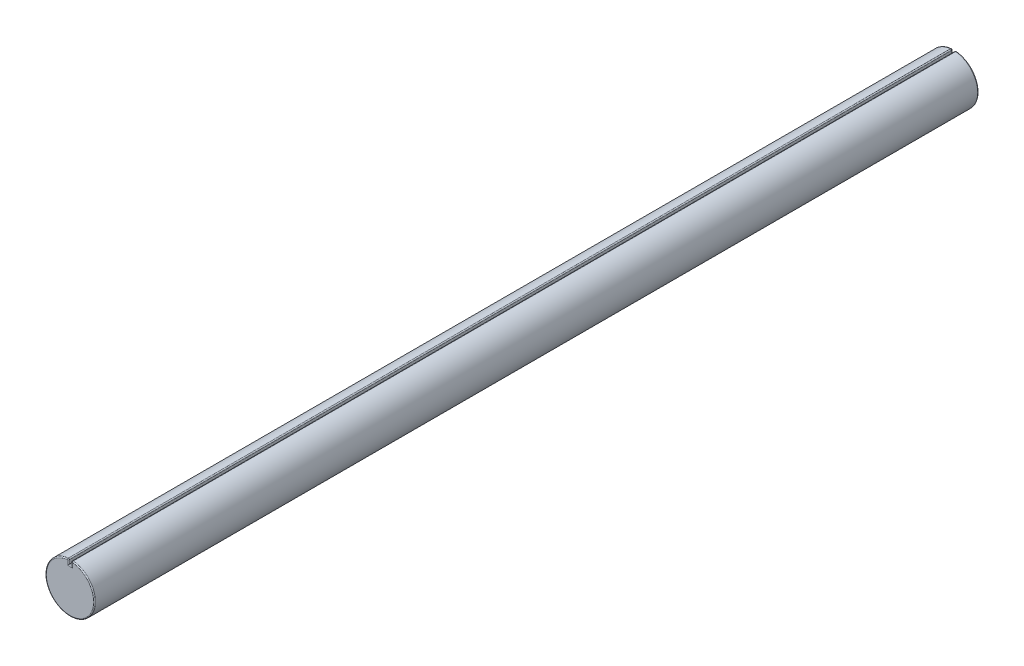
SolidWorks part; units mm, degrees
material "1023 Carbon Steel Sheet (SS)"
ref_plane "Front Plane" through (0, 0, 0) normal (0, 0, 1) x (1, 0, 0)
ref_plane "Top Plane" through (0, 0, 0) normal (0, 1, 0) x (1, 0, 0)
ref_plane "Right Plane" through (0, 0, 0) normal (1, 0, 0) x (0, 0, -1)
sketch "Sketch1" plane through (0, 0, 0) normal (0, 0, 1) x (1, 0, 0)
  circle A0 centre (0, 0) radius 25
  dimension "D1" = 50
extrude "Boss-Extrude1" add sketch "Sketch1" along normal blind 900
sketch "Sketch2" plane through (0, 0, 900) normal (0, 0, 1) x (1, 0, 0)
  line L0 (-28.5345, 0) -> (39.1698, 0) construction
  line L1 (0, -30.6412) -> (0, 33.209) construction
  line L3 (-1.5, 30) -> (1.5, 30)
  line L4 (-1.5, 30) -> (-1.5, 20)
  line L5 (-1.5, 20) -> (1.5, 20)
  line L6 (1.5, 30) -> (1.5, 20)
  line L7 (-1.5, 30) -> (1.5, 20) construction
  line L8 (-1.5, 20) -> (1.5, 30) construction
  point P5 (0, 25)
  dimension "D1" = 25
  dimension "D2" = 3
  dimension "D3" = 10
extrude "Cut-Extrude1" cut sketch "Sketch2" against normal through all both and the other way through all
fillet "Fillet1" radius 1 10 edges at (1.5, 22.4775, 0) (0, 20, 0) (-1.5, 22.4775, 900) (-1.5, 24.955, 450) (0, 20, 900) (1.5, 22.4775, 900) (1.5, 24.955, 450) (0, -25, 0) (-1.5, 22.4775, 0) (0, -25, 900)
equation "\"centerDiameter\" = 50mm"
equation "\"D1@Sketch1\"=\"centerDiameter\""
equation "\"keyWidth\" = 3mm"
equation "\"D2@Sketch2\"=\"keyWidth\""
equation "\"2keyHeight\"= 10mm"
equation "\"D3@Sketch2\"=\"2keyHeight\""
